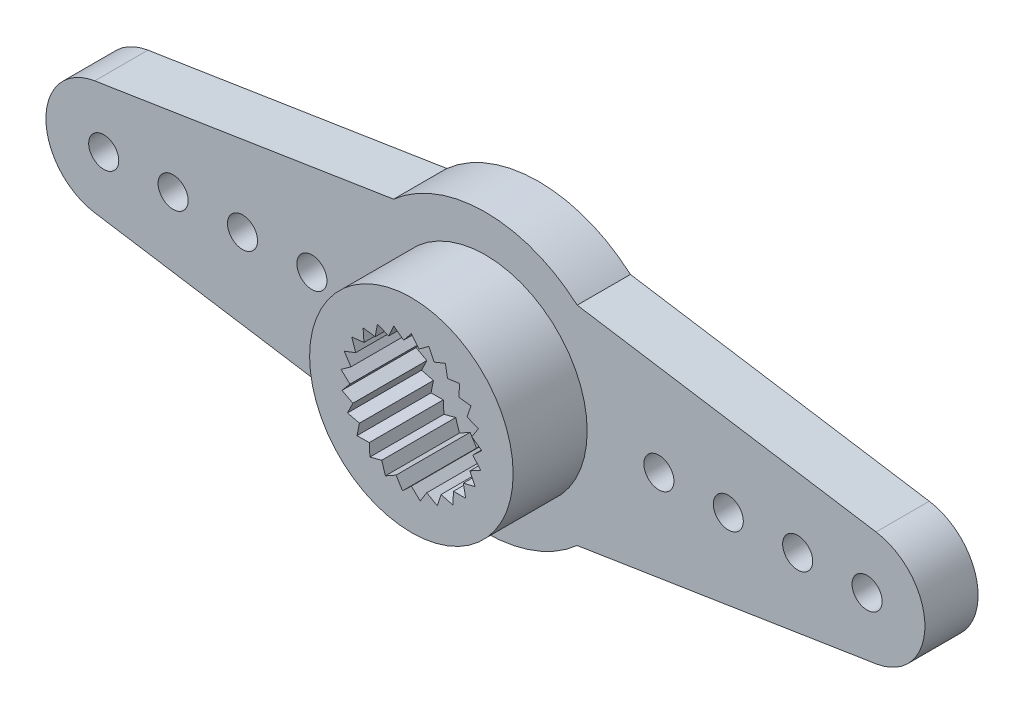
SolidWorks part; units mm, degrees
ref_plane "Front" through (0, 0, 0) normal (0, 0, 1) x (1, 0, 0)
ref_plane "Top" through (0, 0, 0) normal (0, 1, 0) x (1, 0, 0)
ref_plane "Right" through (0, 0, 0) normal (1, 0, 0) x (0, 0, -1)
sketch "Эскиз1" plane through (0, 0, 0) normal (0, 0, 1) x (1, 0, 0)
  line L0 (-3.9686, 4.5) -> (-16.8881, 2.4697)
  line L1 (-19, 4.5) -> (19, 4.5) construction
  line L2 (-19, 4.5) -> (-19, -4.5) construction
  line L3 (-19, -4.5) -> (19, -4.5) construction
  line L4 (19, 4.5) -> (19, -4.5) construction
  line L5 (0, -4.5) -> (0, 4.5) construction
  line L6 (-19, 0) -> (19, 0) construction
  line L7 (-3.9686, -4.5) -> (-16.8881, -2.4697)
  line L8 (3.9686, -4.5) -> (16.8881, -2.4697)
  line L9 (3.9686, 4.5) -> (16.8881, 2.4697)
  circle A0 centre (0, 0) radius 6 construction
  circle A1 centre (-16.5, 0) radius 2.5 construction
  arc A2 (-16.8881, 2.4697) -> (-16.8881, -2.4697) centre (-16.5, 0) ccw
  arc A3 (-3.9686, 4.5) -> (3.9686, 4.5) centre (0, 0) cw
  arc A4 (-3.9686, -4.5) -> (3.9686, -4.5) centre (0, 0) ccw
  circle A5 centre (16.5, 0) radius 2.5 construction
  arc A6 (16.8881, 2.4697) -> (16.8881, -2.4697) centre (16.5, 0) cw
  circle A7 centre (-16.5, 0) radius 0.65
  circle A8 centre (-13.5, 0) radius 0.65
  circle A9 centre (-10.5, 0) radius 0.65
  circle A10 centre (-7.5, 0) radius 0.65
  circle A11 centre (16.5, 0) radius 0.65
  circle A12 centre (7.5, 0) radius 0.65
  circle A13 centre (10.5, 0) radius 0.65
  circle A14 centre (13.5, 0) radius 0.65
  circle A15 centre (0, 0) radius 1.5
  dimension "D1" = 12
  dimension "D4" = 5
  dimension "D5" = 1.3
  dimension "D7" = 3
  dimension "D2" = 9
  dimension "D3" = 38
  dimension "D6" = 4
extrude "Бобышка-Вытянуть1" add sketch "Эскиз1" along normal blind 2.3
sketch "Эскиз2" plane through (0, 0, 2.3) normal (0, 0, 1) x (1, 0, 0)
  line L0 (0, 0) -> (0, 3.05) construction
  line L1 (0, 0) -> (0.3823, 3.0259) construction
  line L2 (0.3334, 2.6394) -> (0, 3.05)
  line L3 (-0.3334, 2.6394) -> (0, 3.05)
  line L4 (0.3334, 2.6394) -> (0.7585, 2.9542)
  line L5 (0.9794, 2.4736) -> (0.7585, 2.9542)
  line L6 (0.9794, 2.4736) -> (1.4693, 2.6727)
  line L7 (1.5638, 2.1523) -> (1.4693, 2.6727)
  line L8 (1.5638, 2.1523) -> (2.0879, 2.2234)
  line L9 (2.0499, 1.6958) -> (2.0879, 2.2234)
  line L10 (2.0499, 1.6958) -> (2.5752, 1.6343)
  line L11 (2.4072, 1.1328) -> (2.5752, 1.6343)
  line L12 (2.4072, 1.1328) -> (2.9007, 0.9425)
  line L13 (2.6133, 0.4985) -> (2.9007, 0.9425)
  line L14 (2.6133, 0.4985) -> (3.044, 0.1915)
  line L15 (2.6552, -0.167) -> (3.044, 0.1915)
  line L16 (2.6552, -0.167) -> (2.996, -0.5715)
  line L17 (2.5302, -0.8221) -> (2.996, -0.5715)
  line L18 (2.5302, -0.8221) -> (2.7597, -1.2986)
  line L19 (2.2463, -1.4255) -> (2.7597, -1.2986)
  line L20 (2.2463, -1.4255) -> (2.3501, -1.9441)
  line L21 (1.8212, -1.9394) -> (2.3501, -1.9441)
  line L22 (1.8212, -1.9394) -> (1.7927, -2.4675)
  line L23 (1.2817, -2.3313) -> (1.7927, -2.4675)
  line L24 (1.2817, -2.3313) -> (1.1228, -2.8358)
  line L25 (0.6616, -2.5768) -> (1.1228, -2.8358)
  line L26 (0.6616, -2.5768) -> (0.3823, -3.0259)
  line L27 (0, -2.6604) -> (0.3823, -3.0259)
  line L28 (0, -2.6604) -> (-0.3823, -3.0259)
  line L29 (-0.6616, -2.5768) -> (-0.3823, -3.0259)
  line L30 (-0.6616, -2.5768) -> (-1.1228, -2.8358)
  line L31 (-1.2817, -2.3313) -> (-1.1228, -2.8358)
  line L32 (-1.2817, -2.3313) -> (-1.7927, -2.4675)
  line L33 (-1.8212, -1.9394) -> (-1.7927, -2.4675)
  line L34 (-1.8212, -1.9394) -> (-2.3501, -1.9441)
  line L35 (-2.2463, -1.4255) -> (-2.3501, -1.9441)
  line L36 (-2.2463, -1.4255) -> (-2.7597, -1.2986)
  line L37 (-2.5302, -0.8221) -> (-2.7597, -1.2986)
  line L38 (-2.5302, -0.8221) -> (-2.996, -0.5715)
  line L39 (-2.6552, -0.167) -> (-2.996, -0.5715)
  line L40 (-2.6552, -0.167) -> (-3.044, 0.1915)
  line L41 (-2.6133, 0.4985) -> (-3.044, 0.1915)
  line L42 (-2.6133, 0.4985) -> (-2.9007, 0.9425)
  line L43 (-2.4072, 1.1328) -> (-2.9007, 0.9425)
  line L44 (-2.4072, 1.1328) -> (-2.5752, 1.6343)
  line L45 (-2.0499, 1.6958) -> (-2.5752, 1.6343)
  line L46 (-2.0499, 1.6958) -> (-2.0879, 2.2234)
  line L47 (-1.5638, 2.1523) -> (-2.0879, 2.2234)
  line L48 (-1.5638, 2.1523) -> (-1.4693, 2.6727)
  line L49 (-0.9794, 2.4736) -> (-1.4693, 2.6727)
  line L50 (-0.9794, 2.4736) -> (-0.7585, 2.9542)
  line L51 (-0.3334, 2.6394) -> (-0.7585, 2.9542)
  circle A0 centre (0, 0) radius 4.4
  circle A1 centre (0, 0) radius 3.05 construction
  circle A2 centre (0, 0) radius 2.65 construction
  point P83 (0, 0)
  dimension "D1" = 8.8
  dimension "D2" = 6.1
  dimension "D3" = 5.3
  dimension "D5" = 25
  dimension "D4" = 7.2
extrude "Бобышка-Вытянуть2" add sketch "Эскиз2" along normal blind 3.2
sketch "Эскиз3" plane through (0, 0, 0) normal (0, 0, -1) x (-1, 0, 0)
  circle A0 centre (0, 0) radius 4.4
  circle A1 centre (0, 0) radius 3.4
  circle A2 centre (0, 0) radius 2.75
  circle M17 centre (0, 0) radius 1.5
  dimension "D1" = 8.8
  dimension "D2" = 6.8
  dimension "D3" = 5.5
extrude "Вырез-Вытянуть1" cut sketch "Эскиз3" against normal blind 1 contours A0 A1 | A2 M17
sketch "Sketch1" plane through (0, 0, 0) normal (0, 0, -1) x (-1, 0, 0)
  line L4 (-3.9686, 4.5) -> (-16.8881, 2.4697)
  line L5 (-16.8881, -2.4697) -> (-3.9686, -4.5)
  line L6 (3.9686, -4.5) -> (16.8881, -2.4697)
  line L7 (16.8881, 2.4697) -> (3.9686, 4.5)
  line L8 (-3.9686, 4.5) -> (-16.8881, 2.4697)
  line L9 (-16.8881, -2.4697) -> (-3.9686, -4.5)
  line L10 (3.9686, -4.5) -> (16.8881, -2.4697)
  line L11 (16.8881, 2.4697) -> (3.9686, 4.5)
  circle A0 centre (16.5, 0) radius 0.65 construction
  circle A1 centre (13.5, 0) radius 0.65 construction
  circle A2 centre (10.5, 0) radius 0.65 construction
  circle A3 centre (7.5, 0) radius 0.65 construction
  arc A4 (3.9686, 4.5) -> (-3.9686, 4.5) centre (0, 0) ccw
  arc A5 (-16.8881, 2.4697) -> (-16.8881, -2.4697) centre (-16.5, 0) ccw
  arc A6 (-3.9686, -4.5) -> (3.9686, -4.5) centre (0, 0) ccw
  arc A7 (16.8881, -2.4697) -> (16.8881, 2.4697) centre (16.5, 0) ccw
  arc A8 (3.9686, 4.5) -> (-3.9686, 4.5) centre (0, 0) ccw
  arc A9 (-16.8881, 2.4697) -> (-16.8881, -2.4697) centre (-16.5, 0) ccw
  arc A10 (-3.9686, -4.5) -> (3.9686, -4.5) centre (0, 0) ccw
  arc A11 (16.8881, -2.4697) -> (16.8881, 2.4697) centre (16.5, 0) ccw
  circle A12 centre (-7.5, 0) radius 0.65 construction
  circle A13 centre (-10.5, 0) radius 0.65 construction
  circle A14 centre (-13.5, 0) radius 0.65 construction
  circle A15 centre (-16.5, 0) radius 0.65 construction
  circle A16 centre (16.5, 0) radius 0.65
  circle A17 centre (13.5, 0) radius 0.65
  circle A18 centre (10.5, 0) radius 0.65
  circle A19 centre (7.5, 0) radius 0.65
  circle A20 centre (-7.5, 0) radius 0.65
  circle A21 centre (-10.5, 0) radius 0.65
  circle A22 centre (-13.5, 0) radius 0.65
  circle A23 centre (-16.5, 0) radius 0.65
  dimension "D1" = 0
